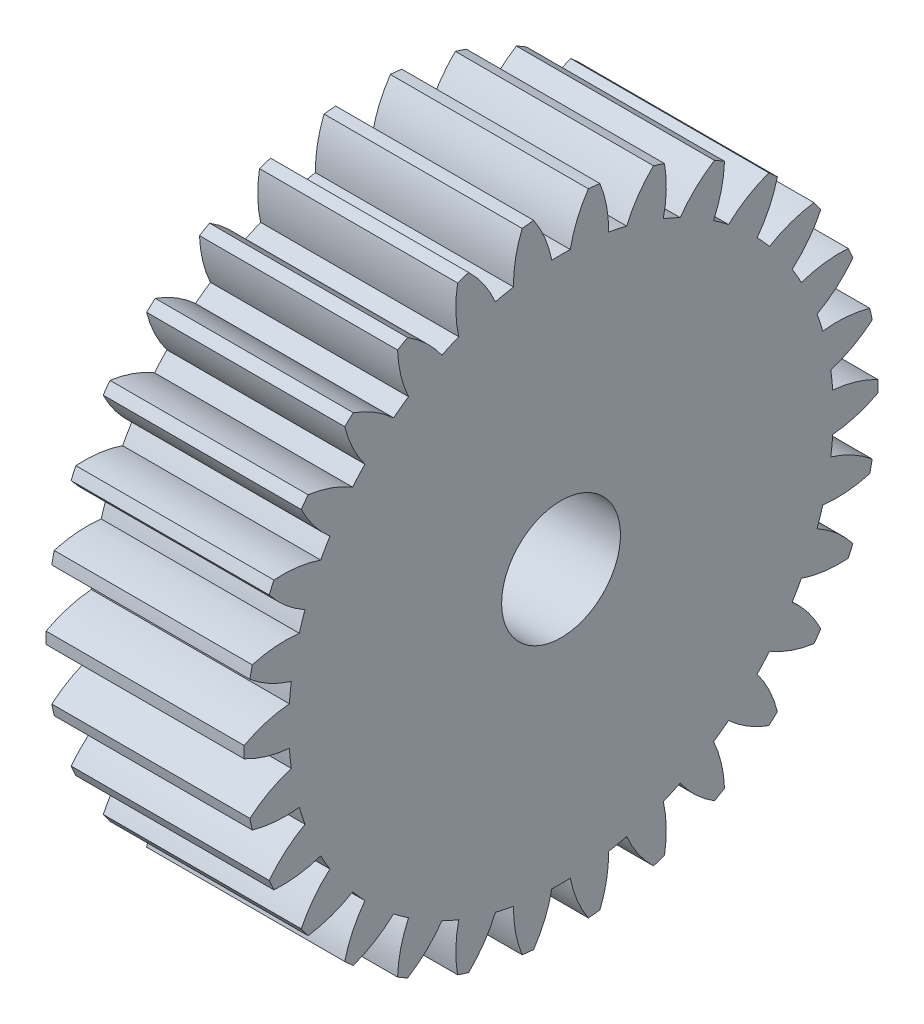
SolidWorks part; units mm, degrees
ref_plane "Plane1" through (0, 0, 0) normal (0, 0, 1) x (1, 0, 0)
ref_plane "Plane2" through (0, 0, 0) normal (0, 1, 0) x (1, 0, 0)
ref_plane "Plane3" through (0, 0, 0) normal (1, 0, 0) x (0, 0, -1)
other "Configuration Table"
sketch "HoldingSke" plane through (0, 0, 0) normal (0, 1, 0) x (1, 0, 0)
  line L0 (0, 0) -> (0.866, -0.5)
  line L1 (-15, 0) -> (100, 0) construction
  line L2 (0, 0) -> (-2.1039, 2.3779)
  line L3 (0, 0) -> (-11.863, 4.5341)
  line L4 (0, 0) -> (7.479, 4.318)
  line L5 (0, 0) -> (-46.8476, -17.4728)
  line L6 (0, 0) -> (-8.2896, -5.593)
  line L7 (-2.1039, 2.3779) -> (8.6586, 51.2059)
  line L8 (-76.2, 54.61) -> (-75.2, 54.61)
  line L9 (-71.009, 38.7566) -> (-53.1078, 45.2721)
  line L10 (-76.2, 71.12) -> (104.1128, 71.12)
  line L11 (0, 0) -> (-10, 0)
  line L12 (-76.2, 101.6) -> (-76.162, 101.6)
  line L13 (24.9733, 27.94) -> (52.9518, 28.4284)
  line L14 (24.9733, 27.94) -> (24.9743, 27.94)
  line L15 (24.9733, 27.94) -> (100.4006, 29.5858)
  line L16 (-63.627, -1) -> (-12.827, -1)
  circle A0 centre (0, 0) radius 3
  circle A1 centre (0, 0) radius 13.749
  circle A2 centre (0, 0) radius 37.5
  circle A3 centre (0, 0) radius 3
  dimension "MHD" = 27.498
  dimension "Hub_dia" = 75
  dimension "Bore" = 6
  dimension "MBD" = 6
  dimension "Num_teeth" = 30
  dimension "Pitch" = 1
  dimension "Overall_len" = 50
  dimension "Show_teeth" = 30
  dimension "Thickness" = 10
  dimension "OAL" = 50.0001
  dimension "T_dim" = 1
  dimension "Ap" = 20
  dimension "H" = 19.05
  dimension "Pitch_radius" = 180.3128
  dimension "Width" = 10
  dimension "Backlash" = 0.038
  dimension "Addendum_fac" = 1
  dimension "Dedendum_fac" = 1.25
  dimension "Clearance_fac" = 0.25
  dimension "Dedendum_add" = 0.001
  dimension "Module" = 1
sketch "BasProSke" plane through (0, 0, 0) normal (0, 1, 0) x (1, 0, 0)
  line L0 (-10, 0) -> (60, 0) construction
  line L1 (0, 0) -> (0, 16)
  line L2 (0, 0) -> (10, 0)
  line L3 (10, 0) -> (10, 16)
  line L4 (10, 16) -> (0, 16)
  dimension "Thickness" = 10
  dimension "Diameter" = 32
revolve "Base-Revolve" add sketch "BasProSke" angle 360 about L0
sketch "TooCutSke" plane through (0, 0, 0) normal (1, 0, 0) x (0, 0, -1)
  line L1 (0, 0) -> (0, 107) construction
  line L2 (0, 0) -> (-0.8515, 14.9758) construction
  line L3 (0, 0) -> (-3.1323, 29.8014) construction
  line L4 (-0.8515, 14.9758) -> (-1.5661, 14.9007) construction
  arc A0 (0.4664, 13.7411) -> (-0.4664, 13.7411) centre (0, 0) ccw
  arc A1 (1.3975, 15.9644) -> (-1.3975, 15.9644) centre (0, 0) ccw
  circle A2 centre (0, 0) radius 15 construction
  circle A3 centre (0, 0) radius 14.0954 construction
  arc A4 (-0.4664, 13.7411) -> (-1.3975, 15.9644) centre (-6.3534, 12.5823) ccw
  arc A5 (1.3975, 15.9644) -> (0.4664, 13.7411) centre (6.3534, 12.5823) ccw
  dimension "Root_dia" = 27.498
  dimension "Overcut_dia" = 32.0508
  dimension "Pitch_dia" = 30
  dimension "Base_dia" = 28.1908
  dimension "Flank_rad" = 6
  dimension "Half_ang" = 6
  dimension "Half_CT" = 0.7185
extrude "ToothCut" cut sketch "TooCutSke" along normal through all
fillet "Breaks" [suppressed] radius 0.02
fillet "RootFillets" [suppressed] radius 0.251
pattern_circular "TeethCuts" count 30 every 12 about axis through (-10, 0, 0) along (1, 0, 0) of "ToothCut", "RootFillets", "Breaks"
sketch "HubNeaOneSke" plane through (0, 0, 0) normal (-1, 0, 0) x (0, 0, 1)
  circle A0 centre (0, 0) radius 13.749
  dimension "Diameter" = 27.498
extrude "HubNearOne" [suppressed] add sketch "HubNeaOneSke" along normal blind 40.0001
sketch "HubNeaBotSke" plane through (0, 0, 0) normal (-1, 0, 0) x (0, 0, 1)
  circle A0 centre (0, 0) radius 13.749
  dimension "Diameter" = 27.498
extrude "HubNearBoth" [suppressed] add sketch "HubNeaBotSke" along normal blind 20
ref_plane "FarPln" through (10, 0, 0) normal (1, 0, 0) x (0, 0, -1)
sketch "HubFarSke" plane through (10, 0, 0) normal (1, 0, 0) x (0, 0, -1)
  circle A0 centre (0, 0) radius 13.749
  dimension "Diameter" = 27.498
extrude "HubFar" [suppressed] add sketch "HubFarSke" along normal blind 20
sketch "BorSke" plane through (0, 0, 0) normal (1, 0, 0) x (0, 0, -1)
  circle A0 centre (0, 0) radius 3
  dimension "Diameter" = 6
extrude "Bore" cut sketch "BorSke" along normal mid plane 100.0001
sketch "KeySke" plane through (0, 0, 0) normal (1, 0, 0) x (0, 0, -1)
  line L0 (-1, 0) -> (-1, 4)
  line L1 (-1, 4) -> (1, 4)
  line L2 (1, 4) -> (1, 0)
  line L3 (0, 0) -> (0, 34) construction
  line L4 (-1, 0) -> (1, 0)
  dimension "Offset" = 4
  dimension "Width" = 2
extrude "Keyway" [suppressed] cut sketch "KeySke" along normal mid plane 100.0001
pattern_circular "Keyway2" [suppressed] count 2 every 90 about axis through (-10, 0, 0) along (1, 0, 0)
equation "' \"Module@HoldingSke\" = 6.35"
equation "' \"Num_teeth@HoldingSke\" = 12"
equation "' \"Ap@HoldingSke\" =  20"
equation "' \"Ap@HoldingSke\" = 20"
equation "' \"Width@HoldingSke\" = 0.5 * 25.4"
equation "' \"Hub_dia@HoldingSke\"= 1 * 25.4"
equation "' \"Hub_dia@HoldingSke\" = 1 * 25.4"
equation "' \"Overall_len@HoldingSke\" = 1.0 * 25.4"
equation "' \"Bore@HoldingSke\" = 0.75 * 25.4"
equation "' \"T_dim@HoldingSke\" = 0.1 * 25.4"
equation "' \"Width@KeySke\" = 0.25 * 25.4"
equation "' \"Show_teeth@HoldingSke\" = 13"
equation "' \"Backlash@HoldingSke\" = 0.009 * 25.4"
equation "' \"Addendum_fac@HoldingSke\" = 1.0"
equation "' \"Dedendum_fac@HoldingSke\" = 1.25"
equation "' \"Dedendum_add@HoldingSke\" = 0.00005 * 25.4"
equation "' \"Clearance_fac@HoldingSke\" = 0.25"
equation "\"Pitch@HoldingSke\" = 1 / \"Module@HoldingSke\""
equation "\"Overcut_dia@TooCutSke\" = (\"Num_teeth@HoldingSke\" + 2 * \"Addendum_fac@HoldingSke\") / \"Pitch@HoldingSke\" + 0.002 * 25.4"
equation "\"Pitch_dia@TooCutSke\" = \"Num_teeth@HoldingSke\" / \"Pitch@HoldingSke\""
equation "\"Base_dia@TooCutSke\" = \"Num_teeth@HoldingSke\" / \"Pitch@HoldingSke\" * cos((\"Ap@HoldingSke\"  * 3.14159265 / 180))"
equation "\"Root_dia@TooCutSke\" = (\"Num_teeth@HoldingSke\" + 2) / \"Pitch@HoldingSke\" - 2 * (\"Addendum_fac@HoldingSke\" + \"Dedendum_fac@HoldingSke\") / \"Pitch@HoldingSke\" - \"Dedendum_add@HoldingSke\" * 2"
equation "\"Half_ang@TooCutSke\" = 180 / \"Num_teeth@HoldingSke\""
equation "\"Half_CT@TooCutSke\" = \"Num_teeth@HoldingSke\" / \"Pitch@HoldingSke\" * sin((3.14159265 / 2 / \"Num_teeth@HoldingSke\")) / 2 - 7 * \"Backlash@HoldingSke\" / 4"
equation "\"Flank_rad@TooCutSke\" = \"Num_teeth@HoldingSke\" / \"Pitch@HoldingSke\" / 5"
equation "\"Radius@RootFillets\" = \"Clearance_fac@HoldingSke\" / \"Pitch@HoldingSke\" + \"Dedendum_add@HoldingSke\""
equation "\"Break_rad@Breaks\" = 0.02 / \"Pitch@HoldingSke\""
equation "\"Thickness@HoldingSke\" = \"Width@HoldingSke\""
equation "\"OAL@HoldingSke\" = \"Thickness@HoldingSke\""
equation "\"MHD@HoldingSke\" = (\"Num_teeth@HoldingSke\" + 2) / \"Pitch@HoldingSke\" - 2 * (\"Addendum_fac@HoldingSke\" + \"Dedendum_fac@HoldingSke\")  / \"Pitch@HoldingSke\" - \"Dedendum_add@HoldingSke\" * 2"
equation "\"MBD@HoldingSke\" = (\"Num_teeth@HoldingSke\" + 2) / \"Pitch@HoldingSke\" - 2 * (\"Addendum_fac@HoldingSke\" + \"Dedendum_fac@HoldingSke\")  / \"Pitch@HoldingSke\" - \"Dedendum_add@HoldingSke\" * 2 - 0.002 * 25.4"
equation "\"MHD@HoldingSke\" = ((sgn( \"MHD@HoldingSke\" - \"Hub_dia@HoldingSke\" )-1)*( \"MHD@HoldingSke\" - \"Hub_dia@HoldingSke\" ))/-2+ \"Hub_dia@HoldingSke\""
equation "\"MBD@HoldingSke\" = ((sgn( \"MBD@HoldingSke\" - \"Bore@HoldingSke\" )-1)*( \"MBD@HoldingSke\" - \"Bore@HoldingSke\" ))/-2+ \"Bore@HoldingSke\""
equation "\"OAL@HoldingSke\" = ((sgn( \"OAL@HoldingSke\" - \"Overall_len@HoldingSke\" )+1)*( \"OAL@HoldingSke\" - \"Overall_len@HoldingSke\" ))/2 + \"Overall_len@HoldingSke\" + 0.000002 * 25.4"
equation "\"Num_teeth@TeethCuts\" = int( \"Show_teeth@HoldingSke\" ) + 1"
equation "\"Num_teeth@TeethCuts\" = ((sgn( \"Num_teeth@TeethCuts\" - \"Num_teeth@HoldingSke\" )-1)*( \"Num_teeth@TeethCuts\" - \"Num_teeth@HoldingSke\" ))/-2+ \"Num_teeth@HoldingSke\""
equation "\"Num_teeth@TeethCuts\" = ((sgn( \"Num_teeth@TeethCuts\" - 2.0)+1)*( \"Num_teeth@TeethCuts\" - 2.0))/2 +2.0"
equation "\"Angle@TeethCuts\" = 360.0 / \"Num_teeth@HoldingSke\""
equation "\"Diameter@BasProSke\" = (\"Num_teeth@HoldingSke\" + 2 * \"Addendum_fac@HoldingSke\") / \"Pitch@HoldingSke\""
equation "\"Thickness@BasProSke\"  = \"Thickness@HoldingSke\""
equation "' \"Fillet_rad@BasProSke\" =  \"Thickness@HoldingSke\" * 0.05"
equation "' \"Fillet_rad@BasProSke\" = \"Thickness@HoldingSke\" * 0.05"
equation "\"MHD@HoldingSke\" = ((sgn( \"MHD@HoldingSke\" - \"Root_dia@TooCutSke\" )-1)*( \"MHD@HoldingSke\" - \"Root_dia@TooCutSke\" ))/-2+ \"Root_dia@TooCutSke\""
equation "\"Diameter@HubNeaOneSke\" = \"MHD@HoldingSke\""
equation "\"Length@HubNearOne\" = \"OAL@HoldingSke\" - \"Thickness@BasProSke\""
equation "\"Diameter@HubNeaBotSke\" = \"MHD@HoldingSke\""
equation "\"Length@HubNearBoth\" = ( \"OAL@HoldingSke\" - \"Thickness@BasProSke\" ) / 2.0"
equation "\"Thickness@FarPln\" = \"Thickness@BasProSke\""
equation "\"Diameter@HubFarSke\" = \"MHD@HoldingSke\""
equation "\"Length@HubFar\" = ( \"OAL@HoldingSke\" - \"Thickness@BasProSke\" ) / 2.0"
equation "\"Diameter@BorSke\" = \"MBD@HoldingSke\""
equation "\"D1@Bore\" = \"OAL@HoldingSke\" * 2.0"
equation "\"D1@Keyway\" = \"OAL@HoldingSke\" * 2.0"
equation "\"Offset@KeySke\" = \"T_dim@HoldingSke\" + \"MBD@HoldingSke\" / 2.0"
